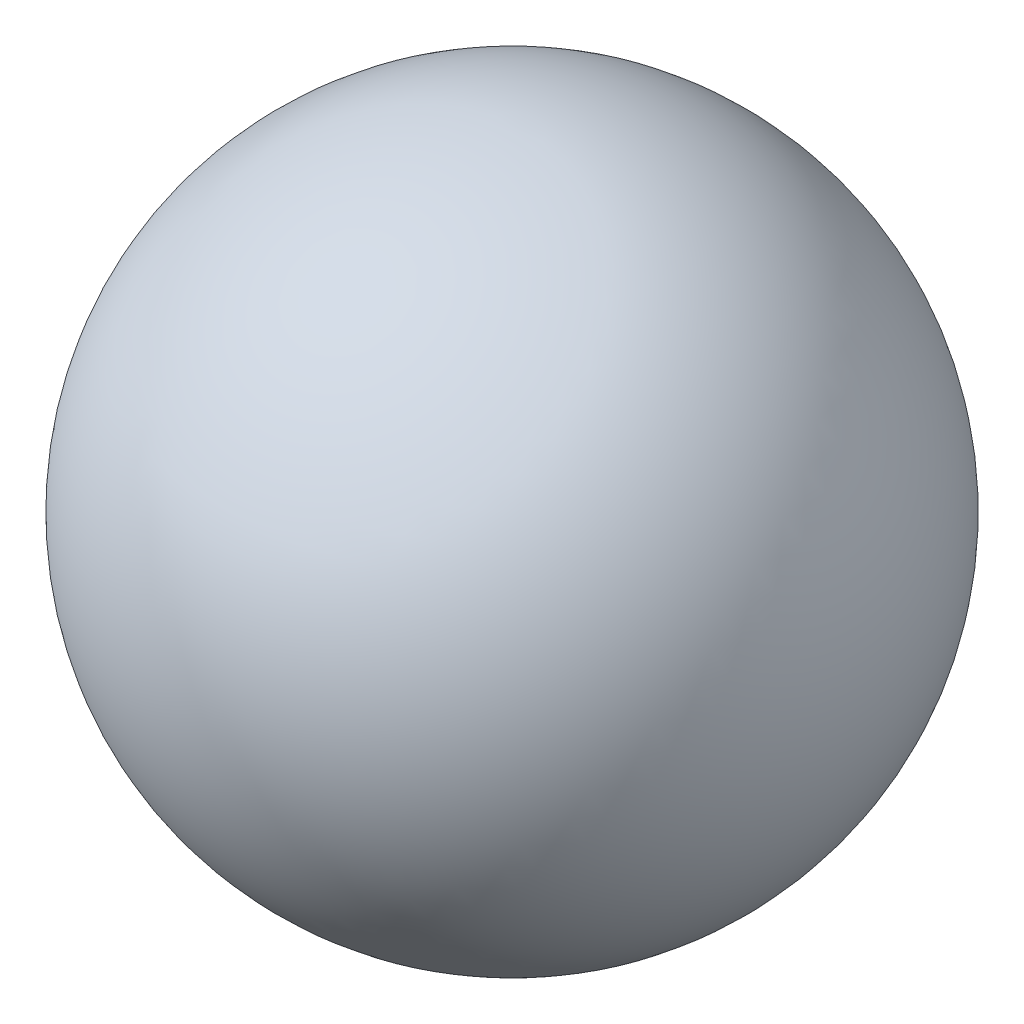
SolidWorks part; units mm, degrees
ref_plane "Plan1" through (0, 0, 0) normal (0, 0, 1) x (1, 0, 0)
ref_plane "Plan2" through (0, 0, 0) normal (0, 1, 0) x (1, 0, 0)
ref_plane "Plan3" through (0, 0, 0) normal (1, 0, 0) x (0, 0, -1)
sketch "Esquisse1" plane through (0, 0, 0) normal (0, 0, 1) x (1, 0, 0)
  line L0 (10.2744, 1.6311) -> (10.2744, 21.6311) construction
  line L1 (10.2744, 1.6311) -> (10.2744, -50.0271) construction
  line L2 (10.2744, 21.6311) -> (10.2744, -18.3689)
  arc A0 (10.2744, 21.6311) -> (10.2744, -18.3689) centre (10.2744, 1.6311) cw
  point P1 (0, 0)
  point P7 (10.2744, 1.6311)
  dimension "D1" = 20
revolve "Révolution1" add sketch "Esquisse1" angle 360 about L1
ref_plane "Plan4" through (0, 0, -20) normal (0, 0, -1) x (-1, 0, 0)
ref_plane "Plan5" through (0, 0, 20) normal (0, 0, 1) x (1, 0, 0)
ref_plane "Plan6" through (0, 0, 0) normal (0, 0, 1) x (1, 0, 0)
sketch "Esquisse9" plane through (0, 0, 0) normal (0, 0, 1) x (1, 0, 0)
  line L0 (4.4032, -17.4877) -> (-9.6088, -0.5271)
  line L1 (-2.6028, -9.0074) -> (23.1515, 12.2696) construction
  line L2 (30.1576, 3.7893) -> (16.1455, 20.7499)
  line L3 (11.4002, 31.6699) -> (37.0983, 0.5641)
  line L4 (-25.2559, 13.2365) -> (5.1052, -23.5135)
  circle A0 centre (10.2744, 1.6311) radius 20 construction
  point P4 (10.2744, 1.6311)
  point P9 (23.1515, 12.2696)
  point P10 (10.2744, 1.6311)
  dimension "D1" = 22
  dimension "D2" = 22
  dimension "D3" = 16.7033
  dimension "D4" = 16.7033
  dimension "D5" = 40
